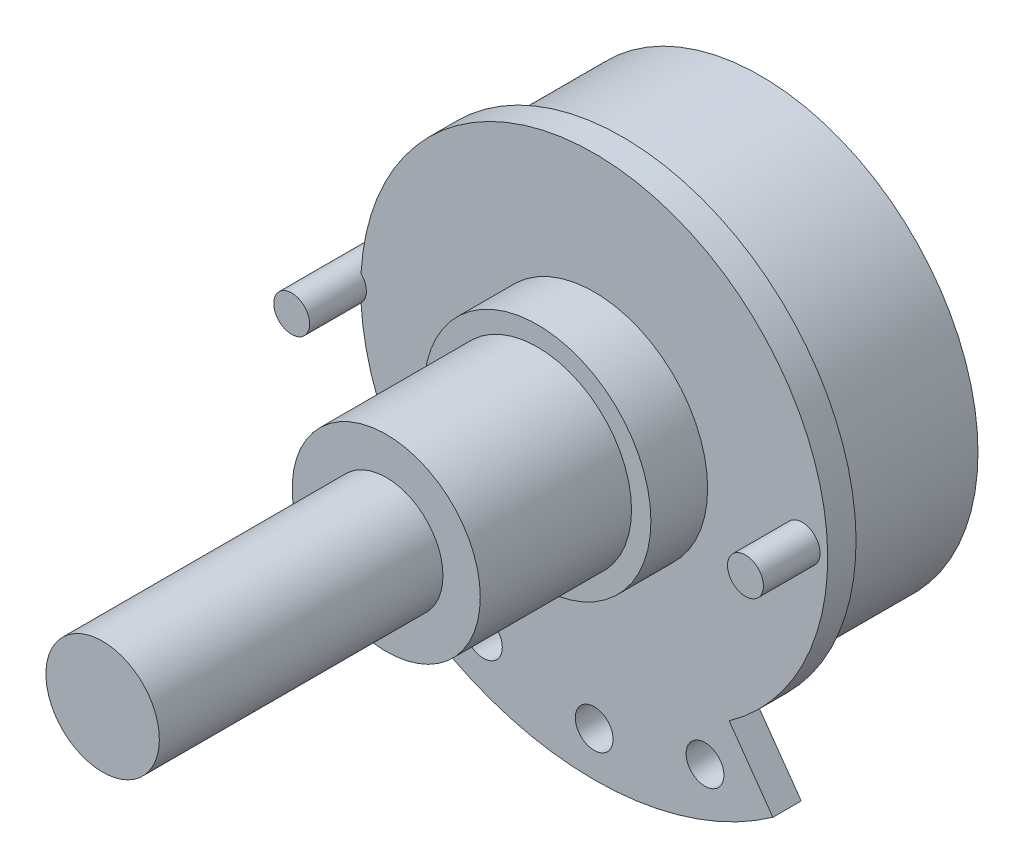
SolidWorks part; units mm, degrees
ref_plane "Front Plane" through (0, 0, 0) normal (0, 0, 1) x (1, 0, 0)
ref_plane "Top Plane" through (0, 0, 0) normal (0, 1, 0) x (1, 0, 0)
ref_plane "Right Plane" through (0, 0, 0) normal (1, 0, 0) x (0, 0, -1)
sketch "Sketch1" plane through (0, 0, 0) normal (0, 0, 1) x (1, 0, 0)
  circle A0 centre (0, 0) radius 11.5
  dimension "D1" = 23
extrude "Extrude1" add sketch "Sketch1" along normal blind 7.3
sketch "Sketch2" plane through (0, 0, 7.3) normal (0, 0, 1) x (1, 0, 0)
  line L0 (-9.45, -13.3424) -> (-7.1381, -10.0782)
  line L1 (7.1381, -10.0782) -> (9.45, -13.3424)
  line L2 (0, 0) -> (0, -17.7937) construction
  arc A0 (7.1381, -10.0782) -> (-7.1381, -10.0782) centre (0, 0) ccw
  arc A1 (-9.45, -13.3424) -> (9.45, -13.3424) centre (0, 0) ccw
  point P3 (0, -16.35)
  dimension "D1" = 24.7
  dimension "D2" = 4
  dimension "D4" = 16.35
  dimension "D3" = 18.9
extrude "Extrude2" add sketch "Sketch2" along normal blind 1.5
sketch "Sketch3" plane through (0, 0, 8.8) normal (0, 0, 1) x (1, 0, 0)
  circle A0 centre (0, -14) radius 1
  circle A1 centre (5.8606, -12.7143) radius 1
  circle A2 centre (-5.8606, -12.7143) radius 1
  circle A3 centre (0, 0) radius 14 construction
  dimension "D1" = 28
  dimension "D2" = 2
  dimension "D3" = 6
  dimension "D4" = 6
extrude "Extrude3" cut sketch "Sketch3" against normal blind 1.5
sketch "Sketch4" plane through (0, 0, 8.8) normal (0, 0, 1) x (1, 0, 0)
  circle A0 centre (0, 0) radius 6
  dimension "D1" = 12
extrude "Extrude4" add sketch "Sketch4" along normal blind 3
sketch "Sketch5" plane through (0, 0, 11.8) normal (0, 0, 1) x (1, 0, 0)
  circle A0 centre (0, 0) radius 4.975
  dimension "D1" = 9.95
extrude "Extrude5" add sketch "Sketch5" along normal blind 8
cosmetic thread "Cosmetic Thread6" parameters "D2"=9
sketch "Sketch6" plane through (0, 0, 19.8) normal (0, 0, 1) x (1, 0, 0)
  circle A0 centre (0, 0) radius 3
  dimension "D1" = 6
extrude "Extrude6" add sketch "Sketch6" along normal blind 15
sketch "Sketch7" plane through (0, 0, 8.8) normal (0, 0, 1) x (1, 0, 0)
  circle A0 centre (11, 0) radius 0.95
  circle A1 centre (-13, 0) radius 0.95
  arc A2 (7.1381, -10.0782) -> (-7.1381, -10.0782) centre (0, 0) ccw construction
  dimension "D2" = 1.9
  dimension "D3" = 11
  dimension "D1" = 24
extrude "Extrude7" add sketch "Sketch7" along normal blind 3 and the other way up to surface
